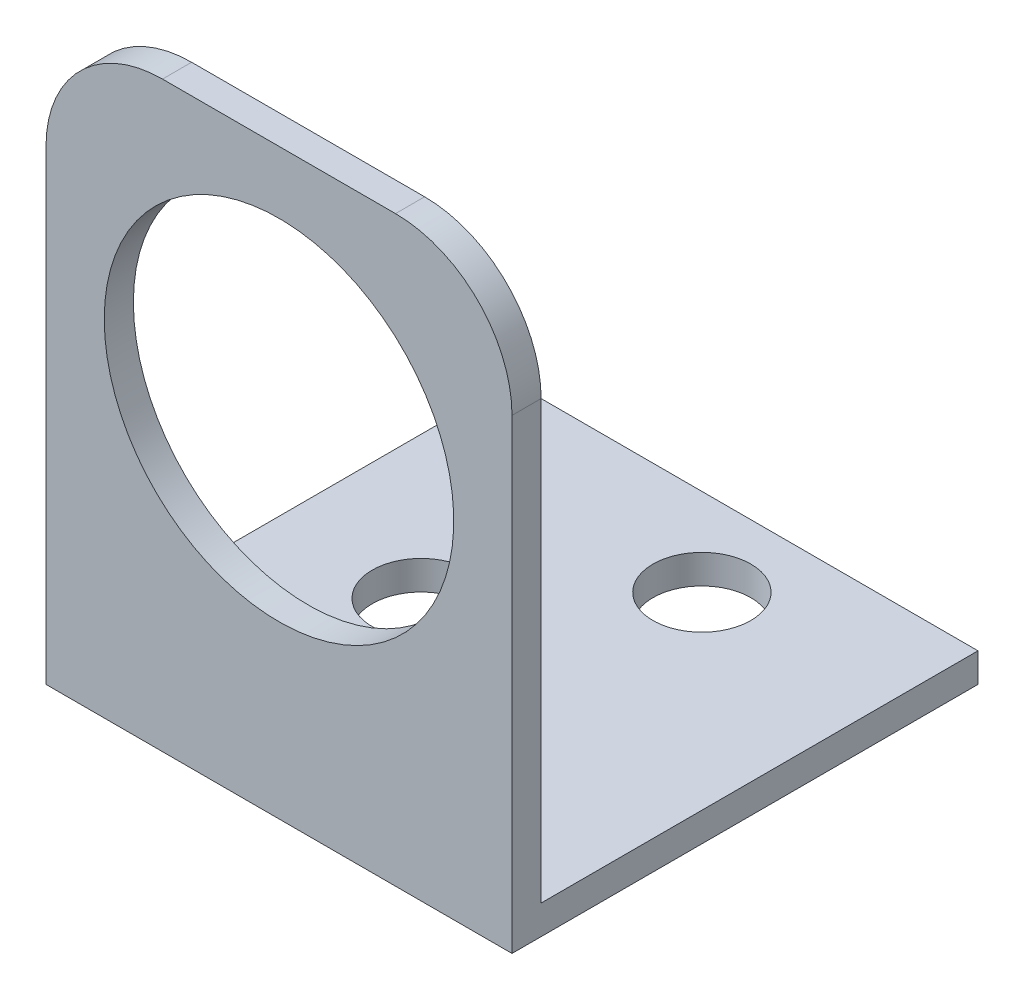
SolidWorks part; units mm, degrees
material "6061-T6 (SS)"
ref_plane "Front" through (0, 0, 0) normal (0, 0, 1) x (1, 0, 0)
ref_plane "Top" through (0, 0, 0) normal (0, 1, 0) x (1, 0, 0)
ref_plane "Right" through (0, 0, 0) normal (1, 0, 0) x (0, 0, -1)
sketch "Sketch1" plane through (0, 0, 0) normal (1, 0, 0) x (0, 0, -1)
  line L0 (1.5875, 1.5875) -> (25.4, 1.5875)
  line L1 (0, 0) -> (25.4, 0)
  line L2 (0, 0) -> (0, 31.75)
  line L5 (1.5875, 1.5875) -> (1.5875, 31.75)
  line L6 (25.4, 0) -> (25.4, 1.5875)
  line L7 (0, 31.75) -> (1.5875, 31.75)
  dimension "D1" = 31.75
  dimension "D2" = 25.4
  dimension "D3" = 1.5875
extrude "Boss-Extrude1" add sketch "Sketch1" along normal blind 25.4
sketch "Sketch2" plane through (0, 0, -1.5875) normal (0, 0, -1) x (-1, 0, 0)
  circle A0 centre (-12.7, 18.8307) radius 9.525 construction
  circle A1 centre (-12.7, 18.8307) radius 9.525
extrude "Cut-Extrude1" cut sketch "Sketch2" against normal up to next
fillet "Fillet1" radius 6.35 2 edges at (25.4, 31.75, -0.7937) (0, 31.75, -0.7937)
sketch "Sketch3" plane through (0, 0, 0) normal (0, -1, 0) x (1, 0, 0)
  line L0 (17.78, -55.7127) -> (17.78, 4.6123) construction
  line L1 (15.113, -20.6375) -> (15.113, -25.4) construction
  line L2 (25.4, -25.4) -> (0, -25.4) construction
  line L3 (5.08, 4.6123) -> (5.08, -55.7127) construction
  line L4 (7.747, -12.7) -> (7.747, -25.4) construction
  circle A0 centre (15.113, -20.6375) radius 2.667
  circle A1 centre (7.747, -12.7) radius 2.667
  dimension "D1" = 5.334
  dimension "D3" = 12.7
  dimension "D2" = 4.7625
extrude "Cut-Extrude2" cut sketch "Sketch3" against normal up to next
